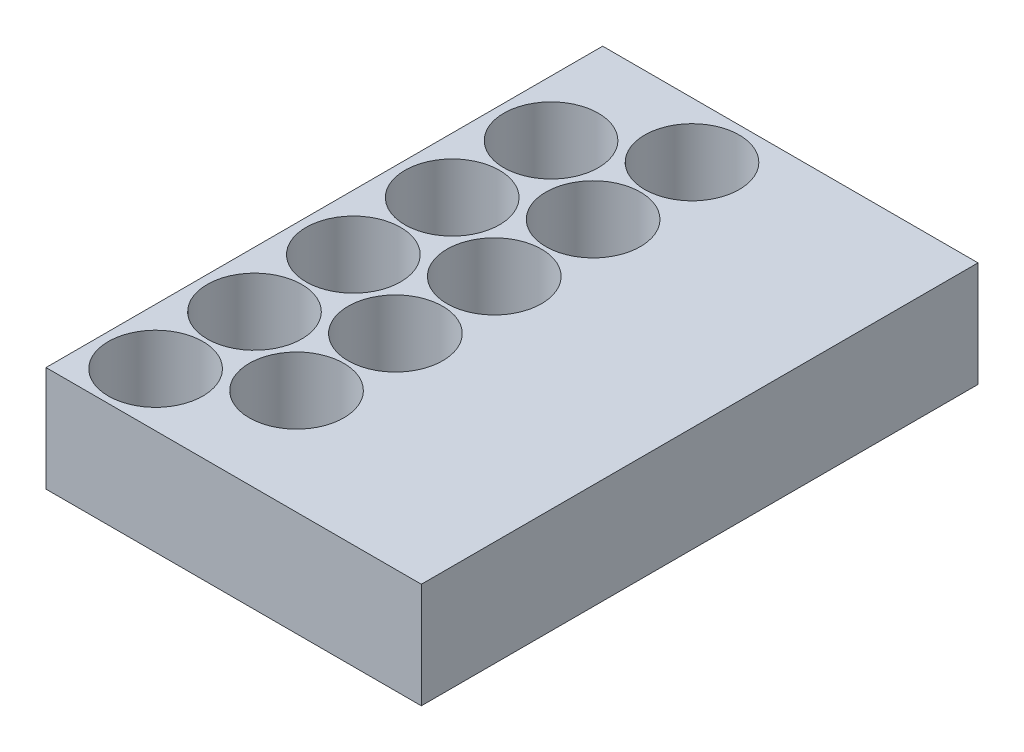
SolidWorks part; units mm, degrees
ref_plane "Front Plane" through (0, 0, 0) normal (0, 0, 1) x (1, 0, 0)
ref_plane "Top Plane" through (0, 0, 0) normal (0, 1, 0) x (1, 0, 0)
ref_plane "Right Plane" through (0, 0, 0) normal (1, 0, 0) x (0, 0, -1)
sketch "Sketch2" plane through (0, 0, 0) normal (0, 1, 0) x (1, 0, 0)
  line L1 (-43.66, -64.75) -> (43.66, -64.75)
  line L2 (-43.66, -64.75) -> (-43.66, 64.75)
  line L3 (-43.66, 64.75) -> (43.66, 64.75)
  line L4 (43.66, -64.75) -> (43.66, 64.75)
  line L5 (-43.66, -64.75) -> (43.66, 64.75) construction
  line L6 (-43.66, 64.75) -> (43.66, -64.75) construction
  point P0 (0, 0)
  dimension "D1" = 87.32
  dimension "D2" = 129.5
extrude "Boss-Extrude1" add sketch "Sketch2" along normal blind 24.5
sketch "Sketch3" plane through (0, 24.5, 0) normal (0, 1, 0) x (1, 0, 0)
  line L1 (-43.66, 64.75) -> (-43.66, -64.75) construction
  line L3 (43.66, 64.75) -> (-43.66, 64.75) construction
  line L4 (-30.66, 39.75) -> (-30.66, 60.8621) construction
  line L5 (-30.66, 39.75) -> (-9.8754, 51.75) construction
  circle A0 centre (-30.66, 39.75) radius 11
  circle A1 centre (-9.8754, 51.75) radius 11
  dimension "D1" = 22
  dimension "D2" = 22
  dimension "D3" = 2
  dimension "D4" = 2
  dimension "D5" = 2
  dimension "D6" = 60
extrude "Cut-Extrude1" cut sketch "Sketch3" against normal through all contours A0 | A1
pattern_linear "LPattern1" count 5 spacing 23 along (0, 0, 1) of "Cut-Extrude1"
